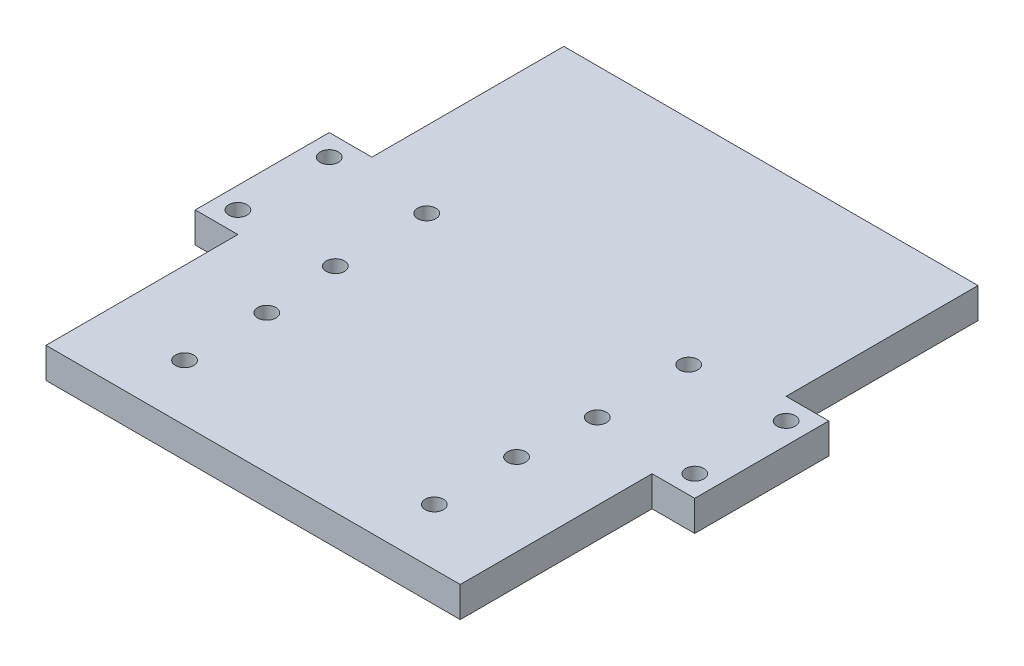
SolidWorks part; units mm, degrees
ref_plane "Front Plane" through (0, 0, 0) normal (0, 0, 1) x (1, 0, 0)
ref_plane "Top Plane" through (0, 0, 0) normal (0, 1, 0) x (1, 0, 0)
ref_plane "Right Plane" through (0, 0, 0) normal (1, 0, 0) x (0, 0, -1)
sketch "Sketch1" plane through (0, 0, 0) normal (0, 1, 0) x (1, 0, 0)
  line L1 (-33, -42.5) -> (33, -42.5)
  line L2 (-33, -42.5) -> (-33, 42.5)
  line L3 (-33, 42.5) -> (33, 42.5)
  line L4 (33, -42.5) -> (33, 42.5)
  line L5 (-33, -42.5) -> (33, 42.5) construction
  line L6 (-33, 42.5) -> (33, -42.5) construction
  point P0 (0, 0)
  dimension "D1" = 66
  dimension "D2" = 85
extrude "Boss-Extrude1" add sketch "Sketch1" along normal blind 5
sketch "Sketch2" plane through (0, 5, 0) normal (0, 1, 0) x (1, 0, 0)
  line L0 (-29.5, 42.5) -> (-29.5, -42.5) construction
  line L4 (33, 42.5) -> (-33, 42.5) construction
  line L5 (-33, -42.5) -> (33, -42.5) construction
  line L6 (-33, 42.5) -> (-33, -42.5) construction
  line L7 (0, 0) -> (0, 15.1289) construction
  circle A2 centre (-29.5, 21.25) radius 1.5
  circle A3 centre (-29.5, -21.25) radius 1.5
  circle A4 centre (29.5, -21.25) radius 1.5
  circle A5 centre (29.5, 21.25) radius 1.5
  dimension "D2" = 3
  dimension "D3" = 3
  dimension "D1" = 3.5
  dimension "D4" = 21.25
  dimension "D5" = 21.25
sketch "Sketch5" plane through (-33, 0, 0) normal (-1, 0, 0) x (0, 0, 1)
  line L1 (-42.5, 0) -> (42.5, 0) construction
  line L2 (-42.5, 5) -> (42.5, 5) construction
  line L3 (-11, 0) -> (11, 0)
  line L5 (-11, 0) -> (11, 0)
  line L6 (-11, 0) -> (-11, 5)
  line L7 (-11, 5) -> (11, 5)
  line L8 (11, 0) -> (11, 5)
  point P8 (0, 0)
  line M2 (-42.5, 0) -> (42.5, 0)
  line M4 (42.5, 5) -> (-42.5, 5)
  dimension "D1" = 22
extrude "Boss-Extrude2" add sketch "Sketch5" along normal blind 7 contours L8 L6 M2 M4
ref_plane "Plane1" through (0, 0, 0) normal (-1, 0, 0) x (0, 0, 1)
mirror "Mirror1" about plane through (0, 0, 0) normal (-1, 0, 0) of "Boss-Extrude2"
sketch "Sketch4" plane through (0, 5, 0) normal (0, 1, 0) x (1, 0, 0)
  line L0 (0, 0) -> (0, -13.5692) construction
  circle A0 centre (-37.5, 7.5) radius 1.5
  circle A1 centre (-21.5, 7.5) radius 1.5
  circle A2 centre (-37.5, -7.5) radius 1.5
  circle A3 centre (-21.5, -7.5) radius 1.5
  circle A4 centre (21.5, -7.5) radius 1.5
  circle A5 centre (37.5, -7.5) radius 1.5
  circle A6 centre (21.5, 7.5) radius 1.5
  circle A7 centre (37.5, 7.5) radius 1.5
  dimension "D1" = 3
  dimension "D3" = 3
  dimension "D4" = 3
  dimension "D6" = 3
  dimension "D2" = 7.5
  dimension "D5" = 15
  dimension "D7" = 16
  dimension "D8" = 21.5
extrude "Cut-Extrude2" cut sketch "Sketch4" against normal blind 10 contours A0 | A1 | A2 | A3 | A6 | A4 | A7 | A5
sketch "Sketch6" plane through (0, 5, 0) normal (0, 1, 0) x (1, 0, 0)
  line L0 (0, 0) -> (0, -5.324) construction
  line L1 (0, 0) -> (-8.8961, 0) construction
  circle A0 centre (-20.5, -26.5) radius 1.5
  circle A1 centre (-21.5, -7.5) radius 1.5 construction
  circle A2 centre (20.5, -26.5) radius 1.5
  circle A3 centre (20.5, 26.5) radius 1.5
  circle A4 centre (-20.5, 26.5) radius 1.5
  dimension "D1" = 3
  dimension "D2" = 19
  dimension "D3" = 1
sketch "Sketch7" plane through (-40, 0, 0) normal (-1, 0, 0) x (0, 0, 1)
  line L1 (-11, 5) -> (11, 5)
  line L2 (-11, 5) -> (-11, 0)
  line L3 (-11, 0) -> (11, 0)
  line L4 (11, 5) -> (11, 0)
extrude "Boss-Extrude3" add sketch "Sketch7" along normal blind 1
sketch "Sketch8" plane through (40, 0, 0) normal (1, 0, 0) x (0, 0, -1)
  line L1 (-11, 5) -> (11, 5)
  line L2 (-11, 5) -> (-11, 0)
  line L3 (-11, 0) -> (11, 0)
  line L4 (11, 5) -> (11, 0)
extrude "Boss-Extrude4" add sketch "Sketch8" along normal blind 1
sketch "Sketch9" plane through (-33, 0, 0) normal (-1, 0, 0) x (0, 0, 1)
  line L1 (-42.5, 5) -> (42.5, 5)
  line L2 (-42.5, 5) -> (-42.5, 0)
  line L3 (-42.5, 0) -> (42.5, 0)
  line L4 (42.5, 5) -> (42.5, 0)
extrude "Boss-Extrude5" add sketch "Sketch9" along normal blind 1
sketch "Sketch10" plane through (33, 0, 0) normal (1, 0, 0) x (0, 0, -1)
  line L1 (-42.5, 5) -> (42.5, 5)
  line L2 (-42.5, 5) -> (-42.5, 0)
  line L3 (-42.5, 0) -> (42.5, 0)
  line L4 (42.5, 5) -> (42.5, 0)
extrude "Boss-Extrude6" add sketch "Sketch10" along normal blind 1
sketch "Sketch11" plane through (0, 5, 0) normal (0, 1, 0) x (1, 0, 0)
  line L0 (-20.5, -42.5) -> (-20.5, -32.4147) construction
  line L1 (-34, -42.5) -> (34, -42.5) construction
  line L2 (-34, -42.5) -> (-34, -11) construction
  line L3 (0, -42.5) -> (0, -21.4326) construction
  line L4 (0, 55) -> (0, -55) construction
  circle A0 centre (-20.5, -33.25) radius 1.5
  circle A1 centre (-20.5, -19.75) radius 1.5
  circle A2 centre (20.5, -33.25) radius 1.5
  circle A3 centre (20.5, -19.75) radius 1.5
  dimension "D2" = 3
  dimension "D4" = 3
  dimension "D1" = 13.5
  dimension "D3" = 9.25
  dimension "D5" = 13.5
extrude "Cut-Extrude3" cut sketch "Sketch11" against normal blind 10
sketch "Sketch12" plane through (0, 5, 0) normal (0, 1, 0) x (1, 0, 0)
  line L0 (-47.1068, -10) -> (44.0422, -10) construction
  circle A0 centre (-21.5, -7.5) radius 1.5 construction
  dimension "D1" = 2.5
